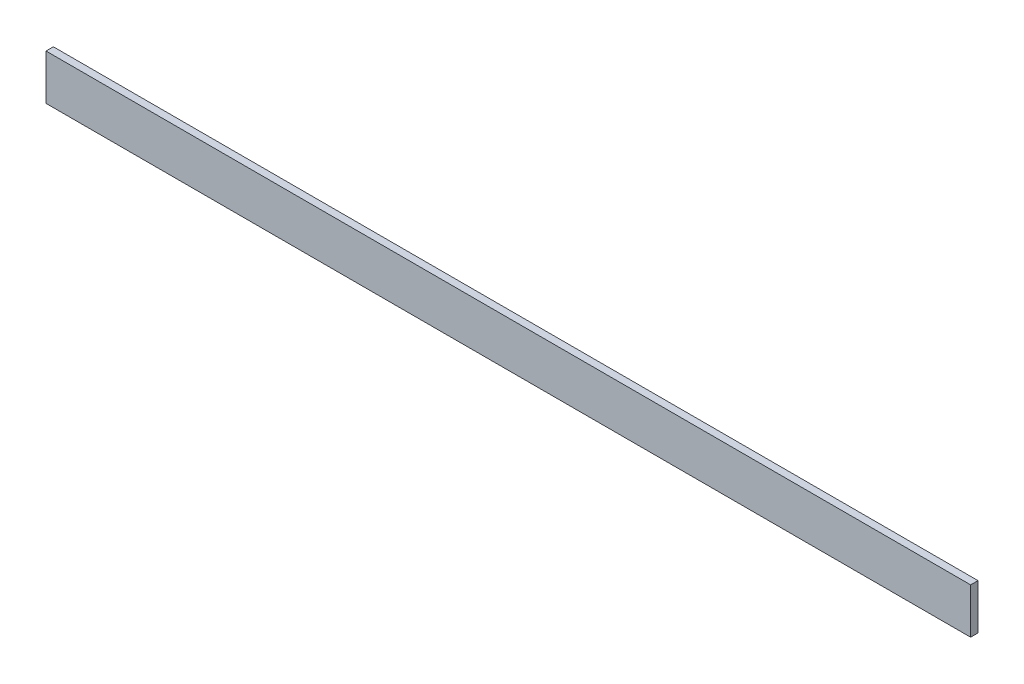
SolidWorks part; units mm, degrees
ref_plane "Front Plane" through (0, 0, 0) normal (0, 0, 1) x (1, 0, 0)
ref_plane "Top Plane" through (0, 0, 0) normal (0, 1, 0) x (1, 0, 0)
ref_plane "Right Plane" through (0, 0, 0) normal (1, 0, 0) x (0, 0, -1)
sketch "Sketch1" plane through (0, 0, 0) normal (0, 0, 1) x (1, 0, 0)
  line L1 (0, 0) -> (4787.9, 0)
  line L2 (0, 0) -> (0, 234.95)
  line L3 (0, 234.95) -> (4787.9, 234.95)
  line L4 (4787.9, 0) -> (4787.9, 234.95)
  dimension "D1" = 234.95
  dimension "D2" = 4787.9
extrude "Boss-Extrude1" add sketch "Sketch1" along normal blind 38.1
